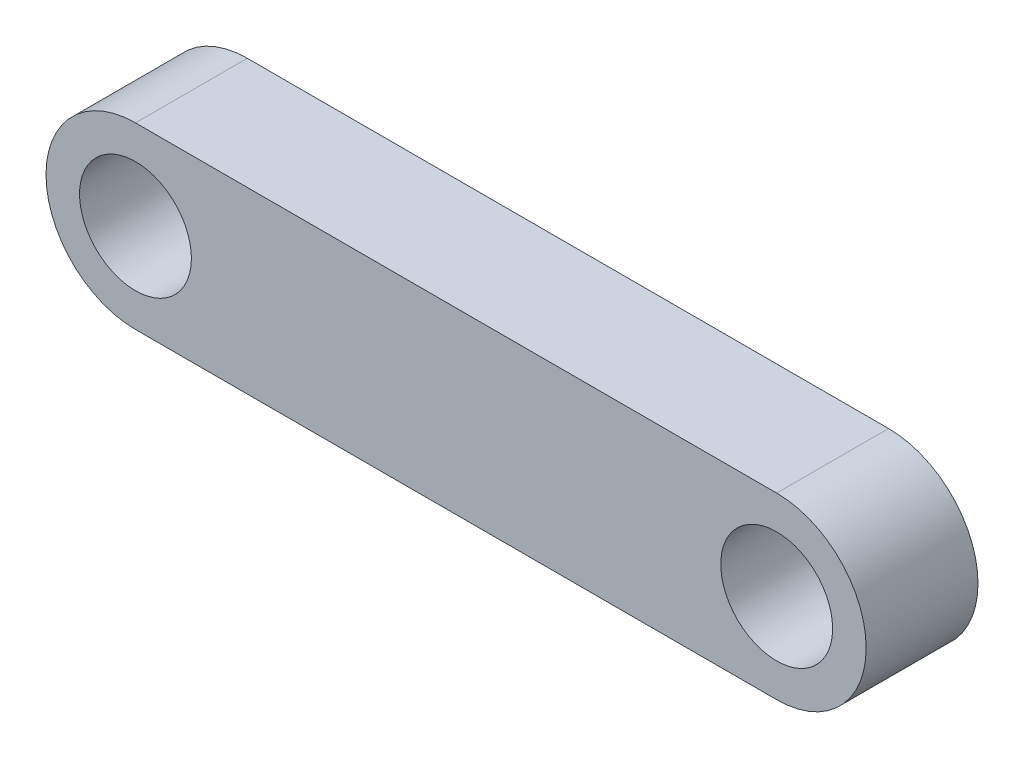
SolidWorks part; units mm, degrees
ref_plane "Plan de face" through (0, 0, 0) normal (0, 0, 1) x (1, 0, 0)
ref_plane "Plan de dessus" through (0, 0, 0) normal (0, 1, 0) x (1, 0, 0)
ref_plane "Plan de droite" through (0, 0, 0) normal (1, 0, 0) x (0, 0, -1)
sketch "Esquisse4" plane through (0, 0, 0) normal (0, 0, 1) x (1, 0, 0)
  line L0 (-19.3326, 33.7871) -> (-2.1329, 33.7871) construction
  line L1 (-19.3326, 36.1871) -> (-2.1329, 36.1871)
  line L2 (-19.3326, 31.3871) -> (-2.1329, 31.3871)
  arc A0 (-19.3326, 36.1871) -> (-19.3326, 31.3871) centre (-19.3326, 33.7871) ccw
  arc A1 (-2.1329, 31.3871) -> (-2.1329, 36.1871) centre (-2.1329, 33.7871) ccw
  circle A2 centre (-19.3326, 33.7871) radius 1.5
  circle A3 centre (-2.1329, 33.7871) radius 1.5
  point P2 (-10.7327, 33.7871)
  dimension "D2" = 3
  dimension "D3" = 2.4
  dimension "D1" = 17.1997
extrude "Boss.-Extru.4" add sketch "Esquisse4" along normal blind 3 separate body
